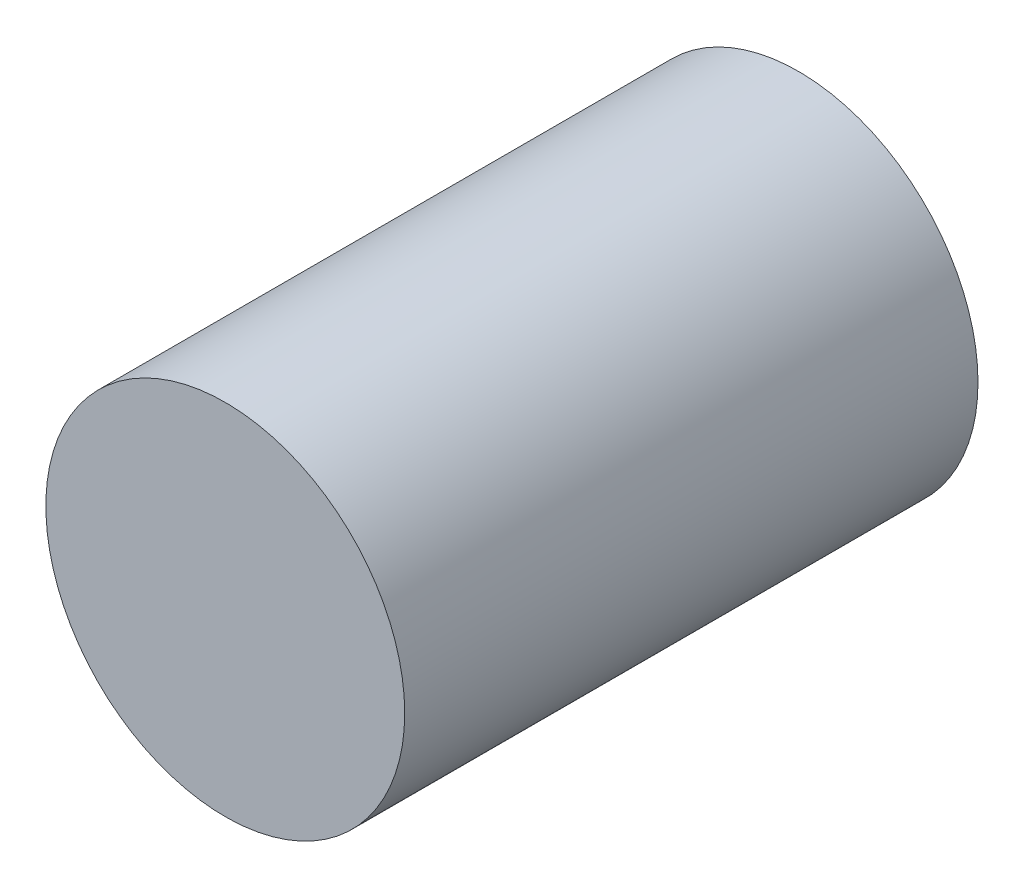
SolidWorks part; units mm, degrees
ref_plane "Front Plane" through (0, 0, 0) normal (0, 0, 1) x (1, 0, 0)
ref_plane "Top Plane" through (0, 0, 0) normal (0, 1, 0) x (1, 0, 0)
ref_plane "Right Plane" through (0, 0, 0) normal (1, 0, 0) x (0, 0, -1)
sketch "Sketch1" plane through (0, 0, 0) normal (0, 0, 1) x (1, 0, 0)
  circle A0 centre (0, 0) radius 15.9
  dimension "D1" = 31.8
extrude "Boss-Extrude1" add sketch "Sketch1" along normal blind 50.8
